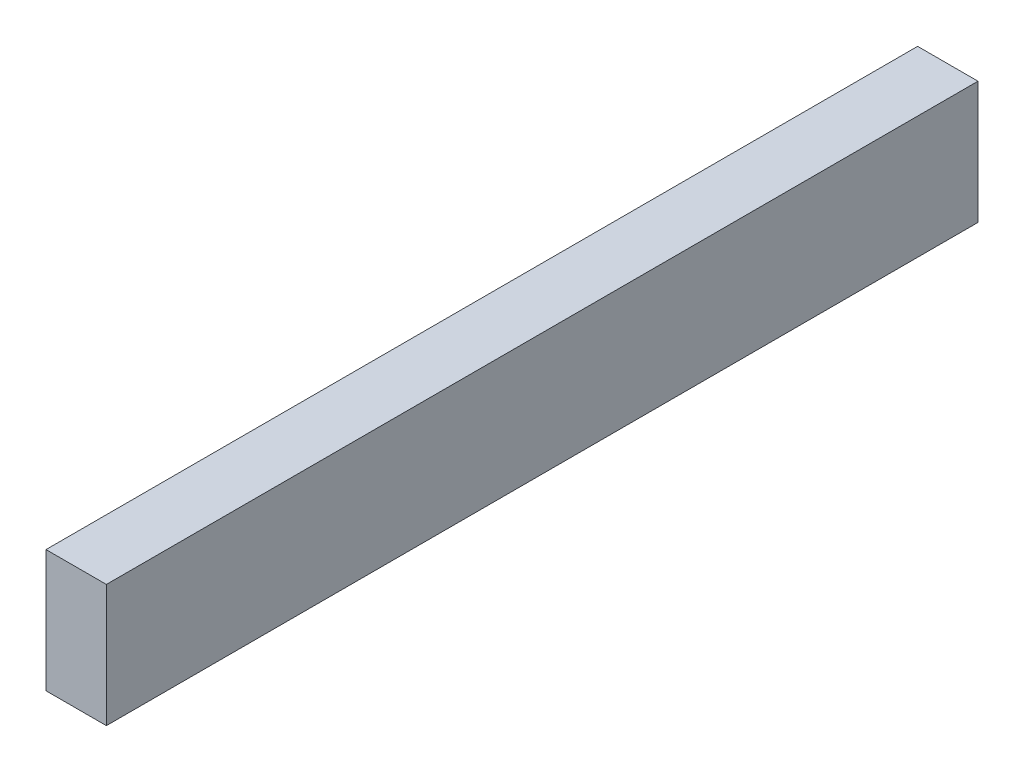
SolidWorks part; units mm, degrees
ref_plane "Front Plane" through (0, 0, 0) normal (0, 0, 1) x (1, 0, 0)
ref_plane "Top Plane" through (0, 0, 0) normal (0, 1, 0) x (1, 0, 0)
ref_plane "Right Plane" through (0, 0, 0) normal (1, 0, 0) x (0, 0, -1)
sketch "Sketch1" plane through (0, 0, 0) normal (0, 0, 1) x (1, 0, 0)
  line L1 (-10.3904, -21.0496) -> (10.3904, -21.0496)
  line L2 (-10.3904, -21.0496) -> (-10.3904, 21.0496)
  line L3 (-10.3904, 21.0496) -> (10.3904, 21.0496)
  line L4 (10.3904, -21.0496) -> (10.3904, 21.0496)
  line L5 (-10.3904, -21.0496) -> (10.3904, 21.0496) construction
  line L6 (-10.3904, 21.0496) -> (10.3904, -21.0496) construction
  point P0 (0, 0)
  dimension "D1" = 20.7809
  dimension "D2" = 42.0991
extrude "Boss-Extrude1" add sketch "Sketch1" along normal blind 300
